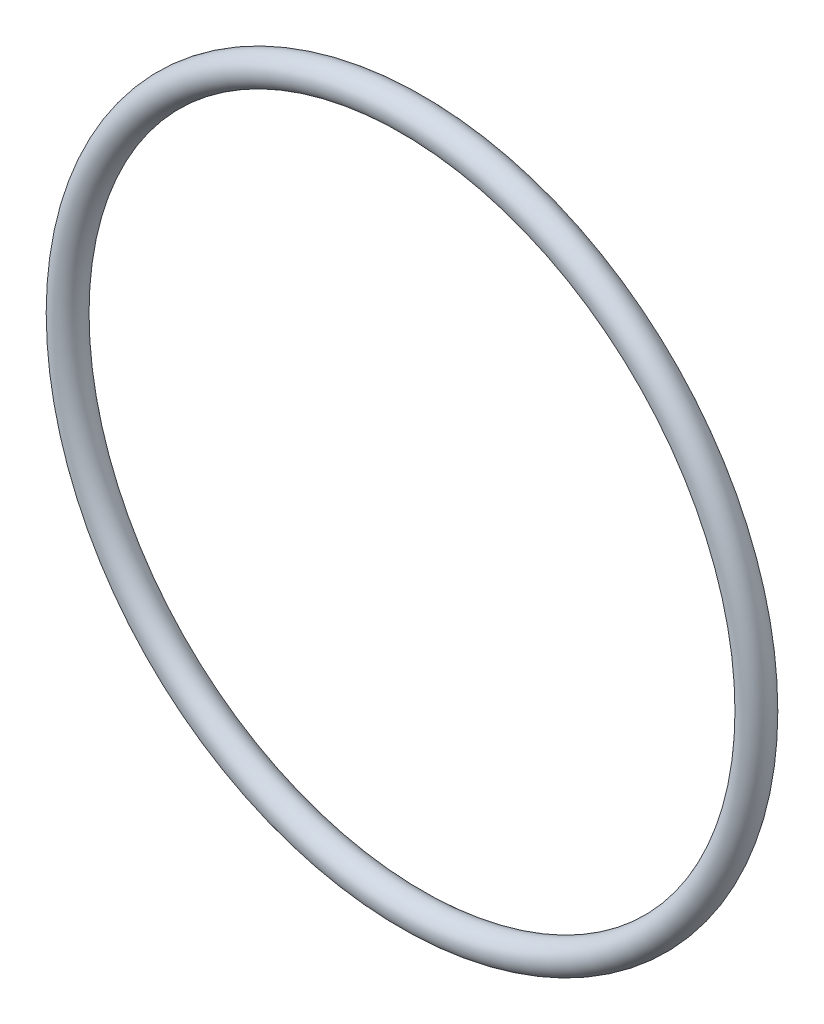
SolidWorks part; units mm, degrees
ref_plane "Front" through (0, 0, 0) normal (0, 0, 1) x (1, 0, 0)
ref_plane "Top" through (0, 0, 0) normal (0, 1, 0) x (1, 0, 0)
ref_plane "Right" through (0, 0, 0) normal (1, 0, 0) x (0, 0, -1)
sketch "Sketch1" plane through (0, 0, 0) normal (1, 0, 0) x (0, -1, 0)
  line L0 (0, -1.3081) -> (0, 1.3081) construction
  line L2 (-34.1287, 0) -> (34.1287, 0) construction
  line L3 (-28.4099, 0) -> (28.4099, 0) construction
  circle A0 centre (29.718, 0) radius 1.3081
  point P9 (28.4099, 0)
  point P10 (31.0261, 0)
  point P13 (29.718, 1.3081)
  point P14 (29.718, -1.3081)
  dimension "Width" = 2.6162
  dimension "ID" = 56.8198
revolve "Revolve1" add sketch "Sketch1" angle 360 about L0
